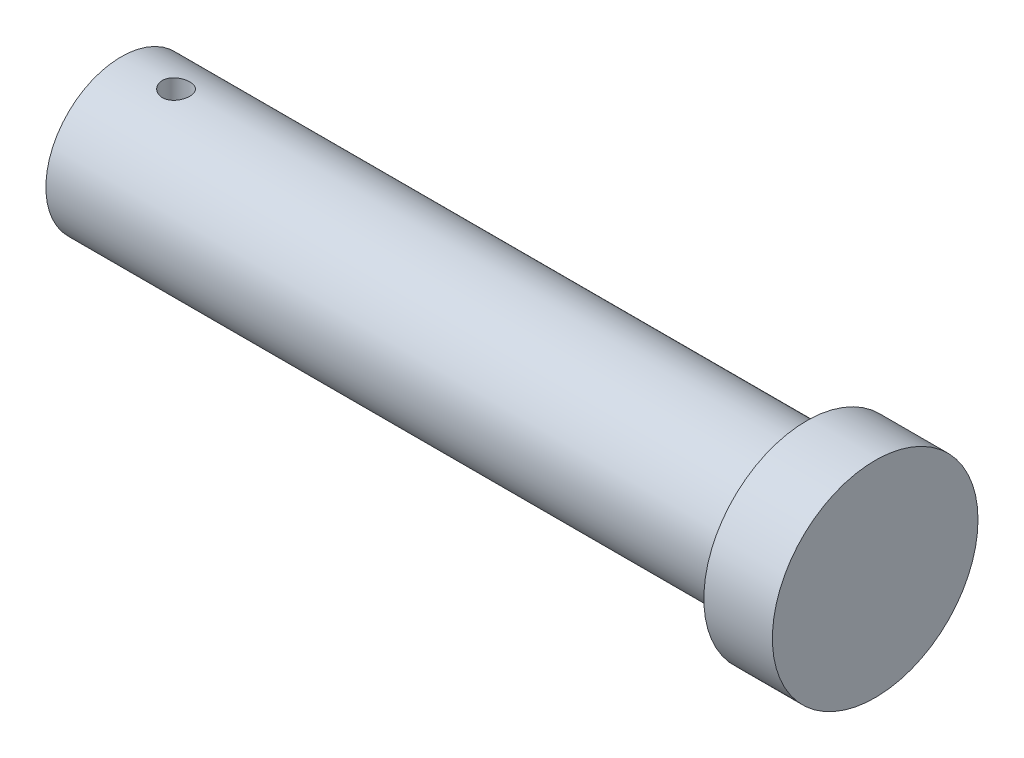
SolidWorks part; units mm, degrees
material "6061-T6 (SS)"
ref_plane "Front Plane" through (0, 0, 0) normal (0, 0, 1) x (1, 0, 0)
ref_plane "Top Plane" through (0, 0, 0) normal (0, 1, 0) x (1, 0, 0)
ref_plane "Right Plane" through (0, 0, 0) normal (1, 0, 0) x (0, 0, -1)
sketch "Sketch1" plane through (0, 0, 0) normal (1, 0, 0) x (0, 0, -1)
  circle A0 centre (0, 0) radius 5.5
  dimension "D1" = 11
extrude "Boss-Extrude1" add sketch "Sketch1" along normal blind 50
sketch "Sketch2" plane through (50, 0, 0) normal (1, 0, 0) x (0, 0, -1)
  circle A0 centre (0, 0) radius 7.5
  dimension "D1" = 15
extrude "Boss-Extrude2" add sketch "Sketch2" along normal blind 5
sketch "Sketch3" plane through (0, 0, 0) normal (0, 1, 0) x (1, 0, 0)
  line L0 (0, 5.5) -> (0, -5.5) construction
  line L1 (50, 5.5) -> (0, 5.5) construction
  circle A0 centre (4, 0) radius 1
  dimension "D1" = 2
  dimension "D2" = 4
  dimension "D3" = 5.5
extrude "Cut-Extrude1" cut sketch "Sketch3" against normal through all both and the other way through all
